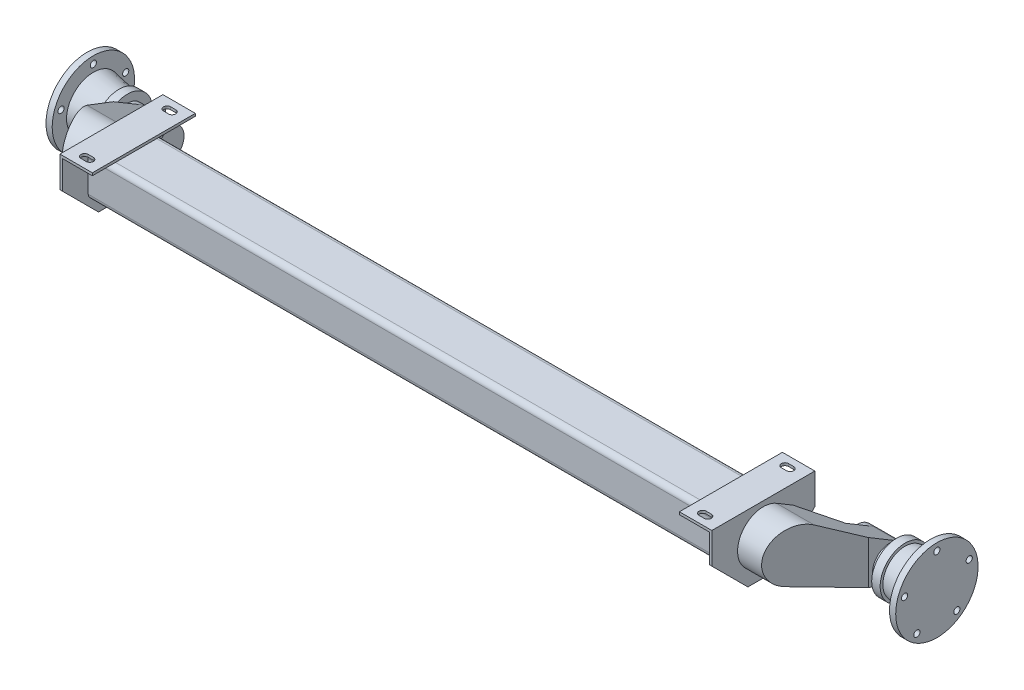
SolidWorks part; units mm, degrees
ref_plane "Front Plane" through (0, 0, 0) normal (0, 0, 1) x (1, 0, 0)
ref_plane "Top Plane" through (0, 0, 0) normal (0, 1, 0) x (1, 0, 0)
ref_plane "Right Plane" through (0, 0, 0) normal (1, 0, 0) x (0, 0, -1)
ref_plane "PlaneFlange" through (825, 0, 0) normal (1, 0, 0) x (0, 0, -1)
sketch "Sketch1" plane through (0, 0, 0) normal (0, 1, 0) x (1, 0, 0)
  line L0 (657.8962, 0) -> (874.947, 0) construction
  line L1 (825, 0) -> (825, 80)
  line L2 (825, -55) -> (825, 55) construction
  line L3 (825, 80) -> (813, 80)
  line L4 (813, 80) -> (813, 52.1025)
  line L5 (813, 52.1025) -> (763.2581, 43.2154)
  line L6 (763.2581, 43.2154) -> (763.2581, 48.4509)
  line L7 (763.2581, 48.4509) -> (746.8512, 48.4509)
  line L8 (746.8512, 48.4509) -> (746.8512, 33.0136)
  line L9 (670, 0) -> (825, 0)
  line L10 (746.8512, 33.0136) -> (670, 33.0136)
  line L11 (670, 33.0136) -> (670, 0)
  dimension "D1" = 160
  dimension "D2" = 12
  dimension "D3" = 670
revolve "Revolve1" add sketch "Sketch1" angle 360 about L0
sketch "Sketch2" plane through (825, 0, 0) normal (1, 0, 0) x (0, 0, -1)
  circle A0 centre (0, 66) radius 6
  circle A1 centre (62.7697, 20.3951) radius 6
  circle A2 centre (38.7938, -53.3951) radius 6
  circle A3 centre (-38.7938, -53.3951) radius 6
  circle A4 centre (-62.7697, 20.3951) radius 6
  point P13 (0, 0)
  dimension "D1" = 12
  dimension "D2" = 66
  dimension "D3" = 5
extrude "Cut-Extrude1" cut sketch "Sketch2" against normal up to next
ref_plane "PlaneMounting" through (0, 127, 0) normal (0, 1, 0) x (1, 0, 0)
sketch "Sketch4" plane through (0, 0, 0) normal (1, 0, 0) x (0, 0, -1)
  line L0 (35.1931, 127) -> (-35.1931, 127) construction
  line L1 (-185, 107) -> (-105, 107)
  line L2 (-195, 97) -> (-195, 37)
  line L3 (-185, 27) -> (-105, 27)
  line L4 (-95, 97) -> (-95, 37)
  line L5 (-145, 107) -> (-145, 27) construction
  arc A0 (-105, 107) -> (-95, 97) centre (-105, 97) cw
  arc A1 (-105, 27) -> (-95, 37) centre (-105, 37) ccw
  arc A2 (-195, 37) -> (-185, 27) centre (-185, 37) ccw
  arc A3 (-185, 107) -> (-195, 97) centre (-185, 97) ccw
  point P14 (-95, 27)
  point P17 (-195, 27)
  dimension "D5" = 10
  dimension "D1" = 20
  dimension "D2" = 100
  dimension "D3" = 100
  dimension "D4" = 145
extrude "Boss-Extrude1" add sketch "Sketch4" along normal blind 633 separate body
sketch "Sketch5" plane through (633, 0, 0) normal (1, 0, 0) x (0, 0, -1)
  line L0 (-145, 27) -> (-145, 163.4716) construction
  line L1 (-185, 27) -> (-105, 27) construction
  line L2 (-245, 127) -> (-45, 127)
  line L3 (178.75, 127) -> (-178.75, 127) construction
  line L4 (-45, 127) -> (-45, 67)
  line L5 (-45, 67) -> (-115, -3)
  line L6 (-115, -3) -> (-175, -3)
  line L7 (-115, -3) -> (-61.185, -3) construction
  line L8 (-245, 67) -> (-175, -3)
  line L9 (-245, 127) -> (-245, 67)
  point P13 (-145, -3)
  point P15 (-145, 127)
  dimension "D1" = 45
  dimension "D2" = 130
  dimension "D3" = 30
  dimension "D4" = 200
extrude "Boss-Extrude2" add sketch "Sketch5" against normal blind 5
sketch "Sketch6" plane through (0, 127, 0) normal (0, 1, 0) x (1, 0, 0)
  line L0 (595, -65) -> (605, -65) construction
  line L1 (633, -45) -> (570, -45)
  line L2 (633, -45) -> (633, -245)
  line L3 (633, -245) -> (570, -245)
  line L4 (570, -45) -> (570, -245)
  line L5 (595, -58) -> (605, -58)
  line L6 (595, -72) -> (605, -72)
  line L7 (570, -145) -> (633, -145) construction
  line L8 (595, -225) -> (605, -225) construction
  line L9 (595, -232) -> (605, -232)
  line L10 (595, -218) -> (605, -218)
  arc A0 (595, -58) -> (595, -72) centre (595, -65) ccw
  arc A1 (605, -72) -> (605, -58) centre (605, -65) ccw
  arc A2 (595, -232) -> (595, -218) centre (595, -225) cw
  arc A3 (605, -218) -> (605, -232) centre (605, -225) cw
  point P8 (600, -65)
  point P18 (600, -225)
  dimension "D1" = 63
  dimension "D2" = 10
  dimension "D3" = 600
  dimension "D4" = 14
  dimension "D5" = 80
extrude "Boss-Extrude3" add sketch "Sketch6" against normal blind 5
sketch "Sketch7" plane through (633, 0, 0) normal (1, 0, 0) x (0, 0, -1)
  line L0 (-145, 107) -> (-145, 27) construction
  line L1 (-185, 107) -> (-105, 107) construction
  line L2 (-105, 27) -> (-185, 27) construction
  line L3 (-95, 67) -> (-145, 67) construction
  line L4 (-95, 97) -> (-95, 37) construction
  line L5 (-119.3637, 109.9276) -> (17.0111, 28.485)
  line L6 (-161.076, 19.6549) -> (-10.6674, -31.4162)
  arc A0 (-119.3637, 109.9276) -> (-161.076, 19.6549) centre (-145, 67) ccw
  arc A1 (-10.6674, -31.4162) -> (17.0111, 28.485) centre (0, 0) ccw
  dimension "D1" = 50
extrude "Boss-Extrude4" add sketch "Sketch7" along normal blind 100 separate body
sketch "Sketch8" plane through (0, 0, 0) normal (0, 1, 0) x (1, 0, 0)
  line L0 (684.126, 52.1722) -> (684.126, -36.0392)
  line L1 (684.126, -36.0392) -> (633, -87.375)
  line L2 (633, 17.0111) -> (633, -119.3637) construction
  line L3 (633, -87.375) -> (621.0832, -87.375)
  line L4 (621.0832, -87.375) -> (621.0832, 52.1722)
  line L5 (621.0832, 52.1722) -> (684.126, 52.1722)
  line L6 (762.557, -18.9272) -> (740.6473, -18.9272)
  line L7 (740.6473, -18.9272) -> (670.9618, -219.8928)
  line L8 (670.9618, -219.8928) -> (762.557, -219.8928)
  line L9 (762.557, -219.8928) -> (762.557, -18.9272)
extrude "Cut-Extrude2" cut sketch "Sketch8" along normal through all and the other way through all
combine bodies "Combine1" operation type add bodies to combine 106 111 102
mirror "Mirror4" about plane through (0, 0, 0) normal (1, 0, 0) of bodies 112
sketch "Sketch9" plane through (0, 0, 0) normal (0, 1, 0) x (1, 0, 0)
  line L0 (969.4625, 0) -> (-969.4625, 0) construction
